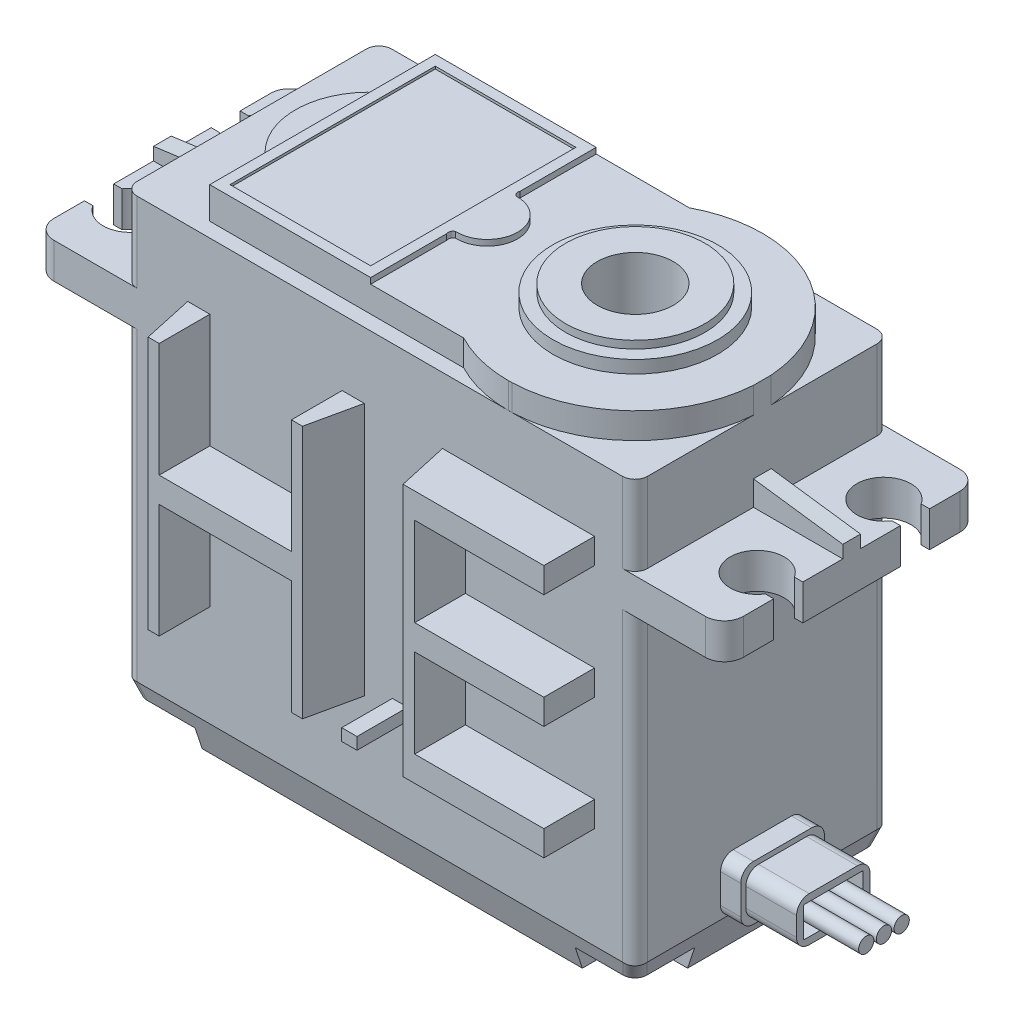
SolidWorks part; units mm, degrees
ref_plane "Ön Düzlem" through (0, 0, 0) normal (0, 0, 1) x (1, 0, 0)
ref_plane "Üst Düzlem" through (0, 0, 0) normal (0, 1, 0) x (1, 0, 0)
ref_plane "Sağ Düzlem" through (0, 0, 0) normal (1, 0, 0) x (0, 0, -1)
sketch "Çizim1" plane through (0, 0, 0) normal (0, 0, 1) x (1, 0, 0)
  line L0 (-48.7593, -35.6983) -> (-8.4593, -35.6983)
  line L1 (-8.4593, -35.6983) -> (-8.4593, -8.5983)
  line L2 (-8.4593, -8.5983) -> (-1.4093, -8.5983)
  line L3 (-1.4093, -8.5983) -> (-1.4093, -5.7983)
  line L4 (-1.4093, -5.7983) -> (-8.4593, -5.7983)
  line L5 (-8.4593, -5.7983) -> (-8.4593, 3.0017)
  line L6 (-8.4593, 3.0017) -> (-48.7593, 3.0017)
  line L7 (-28.6093, 3.0017) -> (-28.6093, -35.6983) construction
  line L8 (-48.7593, -35.6983) -> (-48.7593, -8.5983)
  line L9 (-48.7593, -8.5983) -> (-55.8093, -8.5983)
  line L10 (-55.8093, -8.5983) -> (-55.8093, -5.7983)
  line L11 (-55.8093, -5.7983) -> (-48.7593, -5.7983)
  line L12 (-48.7593, -5.7983) -> (-48.7593, 3.0017)
extrude "Yükseklik-Ekstrüzyon1" add sketch "Çizim1" along normal blind 20.1
ref_plane "Düzlem1" through (0, 0, 10.05) normal (0, 0, 1) x (1, 0, 0)
sketch "Çizim3" plane through (0, 0, 10.05) normal (0, 0, 1) x (1, 0, 0)
  line L0 (-55.8093, -5.7983) -> (-48.7593, -5.7983)
  line L1 (-48.7593, -5.7983) -> (-48.7593, -3.8483)
  line L2 (-48.7593, 3.0017) -> (-48.7593, -5.7983) construction
  line L4 (-55.8093, -5.7983) -> (-55.8093, -4.7983)
  line L5 (-55.8093, -4.7983) -> (-48.7593, -3.8483)
  line L6 (-8.4593, -5.7983) -> (-1.4093, -5.7983)
  line L7 (-1.4093, -5.7983) -> (-1.4093, -4.7983)
  line L8 (-8.4593, -5.7983) -> (-8.4593, -3.8483)
  line L9 (-8.4593, -5.7983) -> (-8.4593, 3.0017) construction
  line L10 (-8.4593, -3.8483) -> (-1.4093, -4.7983)
extrude "Yükseklik-Ekstrüzyon2" add sketch "Çizim3" along normal blind 0.7 and the other way blind 0.7
sketch "Çizim4" plane through (0, 3.0017, 0) normal (0, 1, 0) x (1, 0, 0)
  line L0 (-55.8093, -16.2) -> (-55.1463, -16.2)
  line L1 (-55.8093, -20.1) -> (-55.8093, -10.75) construction
  line L2 (-48.7593, -20.1) -> (-55.8093, -20.1) construction
  line L3 (-55.8093, -16.2) -> (-55.8093, -13.8927)
  line L4 (-55.8093, -13.8927) -> (-55.1463, -13.8927)
  line L5 (-55.8093, -15.0464) -> (-53.3593, -15.0464) construction
  line L11 (-55.8093, -3.9163) -> (-55.1463, -3.9163)
  line L12 (-55.8093, -3.9163) -> (-55.8093, -6.2)
  line L13 (-55.8093, -6.2) -> (-55.1463, -6.2)
  line L14 (-1.4093, -6.2) -> (-2.0723, -6.2)
  line L15 (-1.4093, -3.9) -> (-1.4093, -6.2)
  line L16 (-1.4093, -3.9) -> (-2.0723, -3.9)
  line L17 (-1.4093, -13.9022) -> (-2.0723, -13.9022)
  line L18 (-1.4093, -16.2) -> (-1.4093, -13.9022)
  line L19 (-1.4093, -16.2) -> (-2.0723, -16.2)
  arc A6 (-2.0723, -3.9) -> (-2.0723, -6.2) centre (-3.8652, -5.05) ccw
  arc A7 (-2.0723, -13.9022) -> (-2.0723, -16.2) centre (-3.8659, -15.0511) ccw
  arc A8 (-55.1463, -13.8927) -> (-55.1463, -16.2) centre (-53.3557, -15.0464) cw
  arc A9 (-55.1463, -3.9163) -> (-55.1463, -6.2) centre (-53.3482, -5.0582) cw
  dimension "D1" = 3.9
  dimension "D3" = 2.3
  dimension "D4" = 0.663
  dimension "D5" = 0.663
extrude "Kes-Ekstrüzyon2" cut sketch "Çizim4" against normal blind 50
fillet "Radyus1" radius 1.5 4 edges at (-1.4093, -7.1983, 0) (-1.4093, -7.1983, 20.1) (-55.8093, -7.1983, 20.1) (-55.8093, -7.1983, 0)
fillet "Radyus2" radius 1 8 edges at (-8.4593, -22.1483, 0) (-8.4593, -1.3983, 0) (-48.7593, -22.1483, 0) (-48.7593, -1.3983, 0) (-8.4593, -22.1483, 20.1) (-8.4593, -1.3983, 20.1) (-48.7593, -22.1483, 20.1) (-48.7593, -1.3983, 20.1)
sketch "Çizim5" plane through (0, 3.0017, 0) normal (0, 1, 0) x (1, 0, 0)
  line L0 (-8.4593, -19.1) -> (-8.4593, -1) construction
  line L1 (-18.4593, 0) -> (-48.7603, 0)
  line L2 (-9.4593, 0) -> (-47.7593, 0) construction
  line L3 (-47.7593, 0) -> (-54.3093, 0) construction
  line L4 (-48.7603, 0) -> (-48.7603, -20.1)
  line L5 (-47.7593, -20.1) -> (-54.3093, -20.1) construction
  line L6 (-48.7603, -20.1) -> (-18.4593, -20.1)
  line L7 (-9.4593, -20.1) -> (-47.7593, -20.1) construction
  line L8 (-43.1703, -1.15) -> (-23.1275, -1.15)
  line L9 (-43.1703, -1.15) -> (-43.1703, -5.56)
  line L10 (-18.4593, 0) -> (-1.4093, 0)
  line L11 (-43.1703, -18.95) -> (-23.1275, -18.95)
  line L12 (-43.1703, -18.95) -> (-43.1703, -14.54)
  line L13 (-1.4093, 0) -> (-1.4093, -20.1)
  line L14 (-1.4093, -20.1) -> (-18.4593, -20.1)
  arc A0 (-23.1275, -18.95) -> (-18.4593, -20.1) centre (-18.4593, -10.05) ccw
  arc A1 (-43.1703, -5.56) -> (-43.1703, -14.54) centre (-39.5158, -10.05) ccw
  arc A2 (-18.4593, 0) -> (-23.1275, -1.15) centre (-18.4593, -10.05) ccw
  arc A3 (-18.4593, 0) -> (-18.4593, -20.1) centre (-18.4593, -10.05) cw
  point P0 (-18.4593, -10.05)
  line M14 (-9.4593, 0) -> (-47.7593, 0)
  arc M15 (-47.7593, 0) -> (-48.7593, -1) centre (-47.7593, -1) ccw
  line M16 (-48.7593, -1) -> (-48.7593, -19.1)
  arc M17 (-48.7593, -19.1) -> (-47.7593, -20.1) centre (-47.7593, -19.1) ccw
  line M18 (-47.7593, -20.1) -> (-9.4593, -20.1)
  dimension "D3" = 5.7893
  dimension "D1" = 10
  dimension "D2" = 5.59
  dimension "D4" = 1.15
extrude "Kes-Ekstrüzyon4" cut sketch "Çizim5" against normal blind 2.5 contours A2 A0 L11 L12 A1 L9 L8 M14 M15 M16 M17 M18
sketch "Çizim7" plane through (0, 3.0017, 0) normal (0, 1, 0) x (1, 0, 0)
  line L0 (-43.1703, -5.56) -> (-43.1703, -14.54)
  line L1 (-43.1703, -18.95) -> (-43.1703, -14.54) construction
  arc A0 (-43.1703, -5.56) -> (-43.1703, -14.54) centre (-39.5158, -10.05) ccw construction
  arc A2 (-43.1703, -5.56) -> (-43.1703, -14.54) centre (-39.5158, -10.05) ccw
extrude "Kes-Ekstrüzyon6" cut sketch "Çizim7" against normal blind 0.4
sketch "Çizim8" plane through (0, 3.0017, 0) normal (0, 1, 0) x (1, 0, 0)
  line L0 (-30.4703, -1.15) -> (-23.1275, -1.15)
  line L1 (-30.4703, -1.15) -> (-30.4703, -7.155)
  line L2 (-43.1703, -1.15) -> (-23.1275, -1.15) construction
  line L3 (-43.1703, -1.15) -> (-43.1703, -18.95) construction
  line L4 (-30.4703, -18.95) -> (-30.4703, -12.945)
  line L5 (-30.4703, -18.95) -> (-23.1275, -18.95)
  arc A0 (-30.2662, -12.4481) -> (-30.2662, -7.6519) centre (-30.1703, -10.05) ccw
  arc A1 (-30.4703, -7.155) -> (-30.2662, -7.6519) centre (-30.1198, -7.3014) ccw
  arc A2 (-30.4703, -12.945) -> (-30.2662, -12.4481) centre (-30.1198, -12.7986) cw
  arc A5 (-23.1275, -18.95) -> (-23.1275, -1.15) centre (-18.4593, -10.05) ccw
  point P18 (-23.1275, -1.15)
  point P19 (-23.1275, -18.95)
  dimension "D1" = 12.7
  dimension "D3" = 0.3
extrude "Kes-Ekstrüzyon7" cut sketch "Çizim8" against normal blind 0.46
sketch "Çizim9" plane through (0, 3.0017, 0) normal (0, 1, 0) x (1, 0, 0)
  line L0 (-18.4593, 0) -> (-8.4593, 0)
  line L1 (-2.9093, 0) -> (-9.4593, 0) construction
  line L2 (-8.4593, 0) -> (-8.4593, -9.35)
  line L4 (-8.4593, -20.0999) -> (-8.4593, -10.7499)
  line L5 (-18.4593, -20.0999) -> (-8.4593, -20.0999)
  arc A0 (-18.4593, 0) -> (-8.4593, -9.35) centre (-18.4849, -10.05) cw
  arc A1 (-18.4593, -20.0999) -> (-8.4593, -10.7499) centre (-18.4849, -10.05) ccw
extrude "Kes-Ekstrüzyon8" cut sketch "Çizim9" against normal blind 2.5
sketch "Çizim10" plane through (0, 0, 20.1) normal (0, 0, 1) x (1, 0, 0)
  line L0 (-9.4593, -5.7983) -> (-9.4593, 3.0017) construction
  line L1 (-18.4593, 3.0017) -> (-9.4593, 3.0017)
  line L2 (-18.4593, 3.0017) -> (-18.4593, 0.5017)
  line L3 (-18.4593, 0.5017) -> (-9.4593, 0.5017)
  line L4 (-9.4593, 3.0017) -> (-9.4593, 0.5017)
  line L5 (-8.4593, 0.5017) -> (-18.4593, 0.5017) construction
extrude "Kes-Ekstrüzyon9" cut sketch "Çizim10" against normal blind 0.005
sketch "Çizim11" plane through (0, 3.0017, 0) normal (0, 1, 0) x (1, 0, 0)
  line L0 (-43.1703, -1.15) -> (-43.1703, -5.56) construction
  line L1 (-42.3703, -1.95) -> (-31.2703, -1.95)
  line L2 (-42.3703, -1.95) -> (-42.3703, -18.15)
  line L3 (-42.3703, -18.15) -> (-31.2703, -18.15)
  line L4 (-31.2703, -1.95) -> (-31.2703, -18.15)
  line L5 (-43.1703, -18.95) -> (-23.1275, -18.95) construction
  line L6 (-43.1703, -1.15) -> (-23.1275, -1.15) construction
  line L7 (-30.4703, -1.15) -> (-30.4703, -7.155) construction
  point P6 (-43.1703, -3.355)
  dimension "D1" = 0.8
  dimension "D2" = 0.8
  dimension "D3" = 0.8
  dimension "D4" = 0.8
extrude "Kes-Ekstrüzyon10" cut sketch "Çizim11" against normal blind 0.2
sketch "Çizim12" plane through (0, 2.5417, 0) normal (0, 1, 0) x (1, 0, 0)
  circle A0 centre (-18.4849, -10.05) radius 5.5
  circle A1 centre (-18.4849, -10.05) radius 6.5
extrude "Yükseklik-Ekstrüzyon3" add sketch "Çizim12" along normal blind 1
sketch "Çizim13" plane through (0, 2.5417, 0) normal (0, 1, 0) x (1, 0, 0)
  circle A0 centre (-18.4849, -10.05) radius 5.5
extrude "Yükseklik-Ekstrüzyon4" add sketch "Çizim13" along normal blind 1.6
sketch "Çizim14" plane through (0, 4.1417, 0) normal (0, 1, 0) x (1, 0, 0)
  circle A0 centre (-18.4849, -10.05) radius 3
extrude "Kes-Ekstrüzyon11" cut sketch "Çizim14" against normal blind 10
sketch "Çizim15" plane through (-48.7593, 0, 0) normal (-1, 0, 0) x (0, 0, 1)
  line L0 (20.1, -35.6983) -> (20.1, -32.6983)
  line L1 (20.1, -8.5983) -> (20.1, -35.6983) construction
  line L2 (20.1, -35.6983) -> (19.1, -35.6983)
  line L3 (19.1, -35.6983) -> (1, -35.6983) construction
  line L4 (19.1, -35.6983) -> (20.1, -35.6983) construction
  line L5 (19.1, -35.6983) -> (20.1, -32.6983)
  line L6 (10.05, -28.8885) -> (10.05, 28.8885) construction
  line L7 (0, -35.6983) -> (1, -35.6983)
  line L8 (1, -35.6983) -> (0, -32.6983)
  line L9 (0, -35.6983) -> (0, -32.6983)
extrude "Kes-Ekstrüzyon12" cut sketch "Çizim15" against normal blind 50
sketch "Çizim17" plane through (0, 0, 20.1) normal (0, 0, 1) x (1, 0, 0)
  line L0 (-48.7593, -32.6983) -> (-48.7593, -35.6983)
  line L1 (-48.7593, -35.6983) -> (-48.7593, -8.5983) construction
  line L2 (-48.7593, -35.6983) -> (-47.7593, -35.6983)
  line L3 (-8.4593, -35.6983) -> (-48.7593, -35.6983) construction
  line L4 (-47.7593, -35.6983) -> (-48.7593, -32.6983)
  line L5 (-28.6093, -35.6983) -> (-28.6093, -29.863) construction
  line L6 (-8.4593, -35.6983) -> (-9.4593, -35.6983)
  line L7 (-8.4593, -32.6983) -> (-8.4593, -35.6983)
  line L8 (-9.4593, -35.6983) -> (-8.4593, -32.6983)
extrude "Kes-Ekstrüzyon13" cut sketch "Çizim17" against normal blind 50
fillet "Radyus3" radius 1 4 edges at (-9.1057, -34.6377, 0.6464) (-48.1128, -34.6377, 0.6464) (-9.1057, -34.6377, 19.4536) (-48.1128, -34.6377, 19.4536)
sketch "Çizim18" plane through (0, -35.6983, 0) normal (0, -1, 0) x (1, 0, 0)
  line L0 (-48.7593, 20.1) -> (-43.6093, 20.1)
  line L1 (-54.3093, 20.1) -> (-47.7593, 20.1) construction
  line L2 (-9.4593, 20.1) -> (-47.7593, 20.1) construction
  line L3 (-48.7593, 20.1) -> (-48.7593, 14.95)
  line L4 (-48.7593, 1) -> (-48.7593, 19.1) construction
  line L5 (-48.7593, 14.95) -> (-46.2593, 14.95)
  line L6 (-43.6093, 20.1) -> (-43.6093, 17.6)
  line L7 (-28.6093, 20.1) -> (-28.6093, 9.0698) construction
  line L8 (-48.7593, 10.05) -> (-27.3387, 10.05) construction
  line L9 (-48.7593, 19.1) -> (-48.7593, 1) construction
  line L10 (-48.7593, 5.15) -> (-46.2593, 5.15)
  line L11 (-48.7593, 0) -> (-48.7593, 5.15)
  line L12 (-48.7593, 0) -> (-43.6093, 0)
  line L13 (-43.6093, 0) -> (-43.6093, 2.5)
  line L14 (-8.4593, 14.95) -> (-10.9593, 14.95)
  line L15 (-13.6093, 20.1) -> (-13.6093, 17.6)
  line L16 (-8.4593, 20.1) -> (-8.4593, 14.95)
  line L17 (-8.4593, 20.1) -> (-13.6093, 20.1)
  line L18 (-8.4593, 0) -> (-13.6093, 0)
  line L19 (-13.6093, 0) -> (-13.6093, 2.5)
  line L20 (-8.4593, 0) -> (-8.4593, 5.15)
  line L21 (-8.4593, 5.15) -> (-10.9593, 5.15)
  arc A0 (-43.6093, 17.6) -> (-46.2593, 14.95) centre (-46.2593, 17.6) cw
  arc A1 (-43.6093, 2.5) -> (-46.2593, 5.15) centre (-46.2593, 2.5) ccw
  arc A2 (-13.6093, 17.6) -> (-10.9593, 14.95) centre (-10.9593, 17.6) ccw
  arc A3 (-13.6093, 2.5) -> (-10.9593, 5.15) centre (-10.9593, 2.5) cw
extrude "Kes-Ekstrüzyon14" cut sketch "Çizim18" against normal blind 1.7
sketch "Çizim19" plane through (0, -33.9983, 0) normal (0, -1, 0) x (-1, 0, 0)
  point P0 (46.2593, -17.6)
sketch "Çizim20" plane through (0, -33.9983, 0) normal (0, -1, 0) x (-1, 0, 0)
  line L0 (47.7593, -10.05) -> (44.2993, -10.05) construction
  line L1 (47.7593, -5.15) -> (47.7593, -14.95) construction
  line L2 (28.6093, -19.1) -> (28.6093, -16.25) construction
  line L3 (13.6093, -19.1) -> (43.6093, -19.1) construction
  circle A0 centre (46.2593, -17.6) radius 1.35
  circle A1 centre (46.2593, -16.25) radius 0.1097
  circle A2 centre (10.9593, -17.6) radius 1.35
  circle A3 centre (46.2593, -2.5) radius 1.35
  circle A4 centre (10.9593, -2.5) radius 1.35
  dimension "D1" = 2.7
extrude "Kes-Ekstrüzyon15" cut sketch "Çizim20" against normal blind 32 contours A3 | A2 | A4 | A0
sketch "Çizim21" plane through (-8.4593, 0, 0) normal (1, 0, 0) x (0, 0, -1)
  line L0 (-1, -32.6983) -> (-19.1, -32.6983) construction
  line L1 (-13.35, -32.6983) -> (-6.75, -32.6983)
  line L2 (-13.35, -32.6983) -> (-13.35, -28.3983)
  line L3 (-13.35, -28.3983) -> (-6.75, -28.3983)
  line L4 (-6.75, -32.6983) -> (-6.75, -28.3983)
  line L5 (-10.05, 28.8885) -> (-10.05, -28.8885) construction
  dimension "D1" = 6.6
  dimension "D2" = 4.3
  dimension "D3" = 3.3
extrude "Yükseklik-Ekstrüzyon5" add sketch "Çizim21" along normal blind 1.6
fillet "Radyus4" radius 1 4 edges at (-7.6593, -28.3983, 13.35) (-7.6593, -28.3983, 6.75) (-7.6593, -32.6983, 6.75) (-7.6593, -32.6983, 13.35)
sketch "Çizim22" plane through (-6.8593, 0, 0) normal (1, 0, 0) x (0, 0, -1)
  line L0 (-7.75, -28.3983) -> (-12.35, -28.3983) construction
  line L1 (-12.95, -28.7983) -> (-7.15, -28.7983)
  line L2 (-12.95, -28.7983) -> (-12.95, -32.2983)
  line L3 (-12.95, -32.2983) -> (-7.15, -32.2983)
  line L4 (-7.15, -28.7983) -> (-7.15, -32.2983)
  line L5 (-6.75, -31.6983) -> (-6.75, -29.3983) construction
  line L6 (-12.35, -32.6983) -> (-7.75, -32.6983) construction
  line L7 (-13.35, -29.3983) -> (-13.35, -31.6983) construction
  dimension "D1" = 0.4
  dimension "D2" = 0.4
  dimension "D3" = 0.4
  dimension "D4" = 0.4
extrude "Yükseklik-Ekstrüzyon6" add sketch "Çizim22" along normal blind 4
fillet "Radyus6" radius 1 4 edges at (-4.8593, -28.7983, 7.15) (-4.8593, -32.2983, 7.15) (-4.8593, -32.2983, 12.95) (-4.8593, -28.7983, 12.95)
sketch "Çizim23" plane through (-2.8593, 0, 0) normal (1, 0, 0) x (0, 0, -1)
  line L0 (-8.15, -28.7983) -> (-11.95, -28.7983) construction
  line L1 (-12.4, -29.3483) -> (-7.7, -29.3483)
  line L2 (-12.4, -29.3483) -> (-12.4, -31.7483)
  line L3 (-12.4, -31.7483) -> (-7.7, -31.7483)
  line L4 (-7.7, -29.3483) -> (-7.7, -31.7483)
  line L5 (-7.15, -31.2983) -> (-7.15, -29.7983) construction
  line L6 (-12.95, -29.7983) -> (-12.95, -31.2983) construction
  line L7 (-11.95, -32.2983) -> (-8.15, -32.2983) construction
  dimension "D1" = 0.55
  dimension "D2" = 0.55
  dimension "D3" = 0.55
  dimension "D4" = 0.55
extrude "Kes-Ekstrüzyon17" cut sketch "Çizim23" against normal up to surface (4 mm away) up to face at (-6.8593, -30.5483, 10.05)
fillet "Radyus7" radius 0.1 4 edges at (-4.8593, -31.7483, 12.4) (-4.8593, -31.7483, 7.7) (-4.8593, -29.3483, 7.7) (-4.8593, -29.3483, 12.4)
sketch "Çizim24" plane through (-6.8593, 0, 0) normal (1, 0, 0) x (0, 0, -1)
  line L0 (-12.4, -29.4483) -> (-12.4, -31.6483) construction
  circle A0 centre (-11.45, -30.5483) radius 0.6
  circle A1 centre (-10.05, -30.5483) radius 0.6
  circle A2 centre (-8.65, -30.5483) radius 0.6
  dimension "D1" = 1.2
  dimension "D2" = 1.2
  dimension "D3" = 1.2
  dimension "D4" = 1.4
  dimension "D5" = 1.4
  dimension "D6" = 0.95
extrude "Yükseklik-Ekstrüzyon7" add sketch "Çizim24" along normal blind 8
sketch "Çizim25" plane through (0, 0, 20.1) normal (0, 0, 1) x (1, 0, 0)
  line L0 (-48.7593, -32.6983) -> (-48.7593, -8.5983) construction
  line L1 (-43.7593, -4.6983) -> (-42.0093, -4.6983)
  line L2 (-43.7593, -4.6983) -> (-43.7593, -24.6983)
  line L3 (-43.7593, -24.6983) -> (-42.0093, -24.6983)
  line L4 (-42.0093, -4.6983) -> (-42.0093, -24.6983)
  line L5 (-42.0093, -13.6983) -> (-31.571, -13.6983)
  line L6 (-43.7593, -10.6104) -> (-43.7593, -12.6104)
  line L7 (-42.0093, -15.6983) -> (-31.571, -15.6983)
  line L8 (-31.571, -13.6983) -> (-31.571, -15.6983)
  line L9 (-31.571, -4.6983) -> (-29.821, -4.6983)
  line L10 (-31.571, -4.6983) -> (-31.571, -24.6983)
  line L11 (-31.571, -24.6983) -> (-29.821, -24.6983)
  line L12 (-29.821, -4.6983) -> (-29.821, -24.6983)
  line L14 (-10.8802, -1.6104) -> (-10.8802, -1.6107)
  line L29 (-9.4593, -32.6983) -> (-47.7593, -32.6983) construction
  line L31 (-23.6507, -4.6983) -> (-11.6507, -4.6983)
  line L32 (-23.6507, -4.6983) -> (-23.6507, -6.6983)
  line L33 (-21.8411, -6.6983) -> (-11.6507, -6.6983)
  line L34 (-11.6507, -4.6983) -> (-11.6507, -6.6983)
  line L35 (-23.6507, -4.6983) -> (-21.8411, -4.6983)
  line L36 (-23.6507, -4.6983) -> (-23.6507, -24.6822)
  line L37 (-23.6507, -24.6822) -> (-21.8411, -24.6822)
  line L38 (-21.8411, -4.6983) -> (-21.8411, -24.6822)
  line L39 (-23.6507, -24.6822) -> (-11.6507, -24.6822)
  line L40 (-23.6507, -24.6822) -> (-23.6507, -22.6822)
  line L41 (-21.8411, -22.6822) -> (-11.6507, -22.6822)
  line L42 (-11.6507, -24.6822) -> (-11.6507, -22.6822)
  line L43 (-21.8411, -13.6983) -> (-11.6507, -13.6983)
  line L44 (-23.6507, -13.6983) -> (-23.6507, -15.6983)
  line L45 (-21.8411, -15.6983) -> (-11.6507, -15.6983)
  line L46 (-11.6507, -13.6983) -> (-11.6507, -15.6983)
  line L47 (-27.6022, -24.6983) -> (-26.3958, -24.6983)
  line L48 (-27.6022, -24.6983) -> (-27.6022, -23.7545)
  line L49 (-27.6022, -23.7545) -> (-26.3958, -23.7545)
  line L50 (-26.3958, -24.6983) -> (-26.3958, -23.7545)
  point P42 (0, 0)
  dimension "D1" = 1.75
  dimension "D2" = 2
  dimension "D3" = 20
  dimension "D4" = 9
  dimension "D5" = 0
  dimension "D6" = 1.75
  dimension "D7" = 5
  dimension "D8" = 8
  dimension "D9" = 2
  dimension "D10" = 12
  dimension "D11" = 12
  dimension "D12" = 12
  dimension "D13" = 2
  dimension "D14" = 2
extrude "Yükseklik-Ekstrüzyon9" add sketch "Çizim25" along normal blind 4 contours L4 L1 L2 L3 | L8 L5 L4 L7 | L12 L9 L10 L8 L11 | L38 L31 L32 L36 L37 | L46 L43 L38 L45 | L31 L38 L33 L34 | L39 L42 L41 L38 | L47 L50 L49 L48
sketch "Çizim26" plane through (0, -24.6983, 0) normal (0, -1, 0) x (1, 0, 0)
  line L0 (-43.7593, 24.1) -> (-43.7593, 20.1)
  line L1 (-43.7593, 20.1) -> (-42.8843, 24.1)
  line L2 (-43.7593, 24.1) -> (-42.0093, 24.1) construction
  line L3 (-42.8843, 24.1) -> (-43.7593, 24.1)
  line L4 (-30.696, 24.1) -> (-29.821, 24.1)
  line L5 (-31.571, 24.1) -> (-29.821, 24.1) construction
  line L6 (-29.821, 24.1) -> (-29.821, 20.1)
  line L7 (-29.821, 20.1) -> (-30.696, 24.1)
extrude "Kes-Ekstrüzyon18" cut sketch "Çizim26" against normal blind 21
sketch "Çizim27" plane through (0, -24.6822, 0) normal (0, -1, 0) x (1, 0, 0)
  line L0 (-23.6507, 24.1) -> (-22.7636, 24.1)
  line L1 (-23.6507, 24.1) -> (-11.6507, 24.1) construction
  line L2 (-22.7636, 24.1) -> (-23.6507, 20.1)
  line L3 (-23.6507, 20.1) -> (-23.6507, 24.1)
extrude "Kes-Ekstrüzyon19" cut sketch "Çizim27" against normal blind 21
